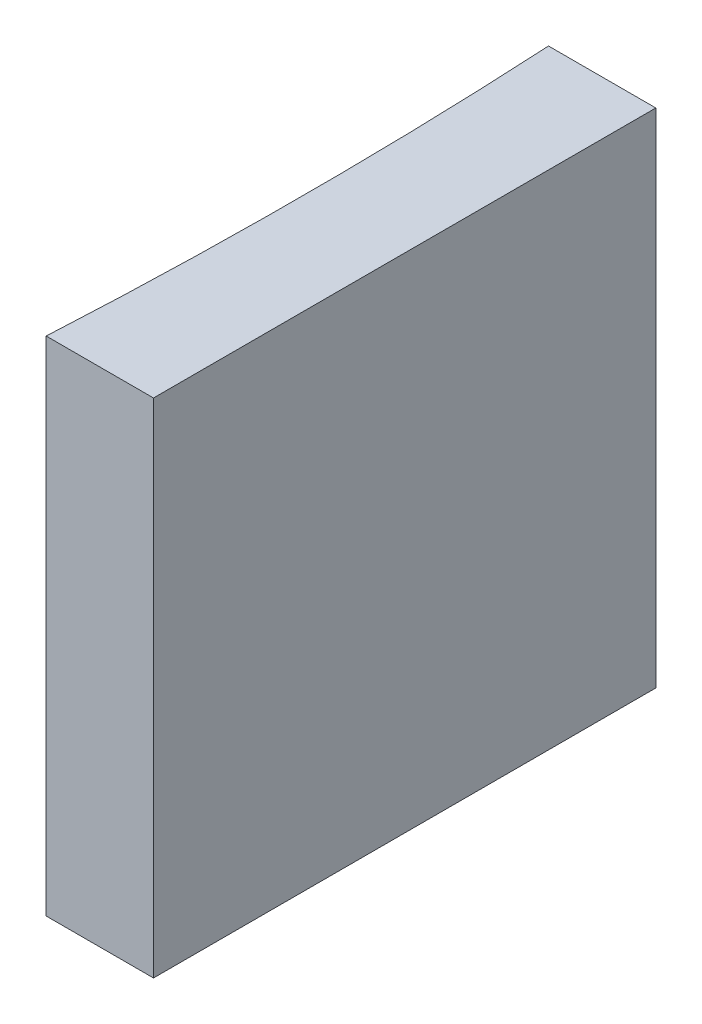
SolidWorks part; units mm, degrees
ref_plane "前视基准面" through (0, 0, 0) normal (0, 0, 1) x (1, 0, 0)
ref_plane "上视基准面" through (0, 0, 0) normal (0, 1, 0) x (1, 0, 0)
ref_plane "右视基准面" through (0, 0, 0) normal (1, 0, 0) x (0, 0, -1)
sketch "草图1" plane through (0, 0, 0) normal (0, 1, 0) x (1, 0, 0)
  line L0 (0, 0) -> (0, -10)
  line L1 (0, 0) -> (-2.1364, 0)
  line L2 (0, -10) -> (-2.1364, -10)
  line L3 (21.2259, -5) -> (-21.2259, -5) construction
  arc A0 (-2.1364, -10) -> (-2.1364, 0) centre (-93.7, -5) ccw
  point P7 (-2, -5)
  point P8 (0, -5)
  dimension "D2" = 91.7
  dimension "D3" = 2
  dimension "D1" = 10
extrude "凸台-拉伸1" add sketch "草图1" along normal blind 10
